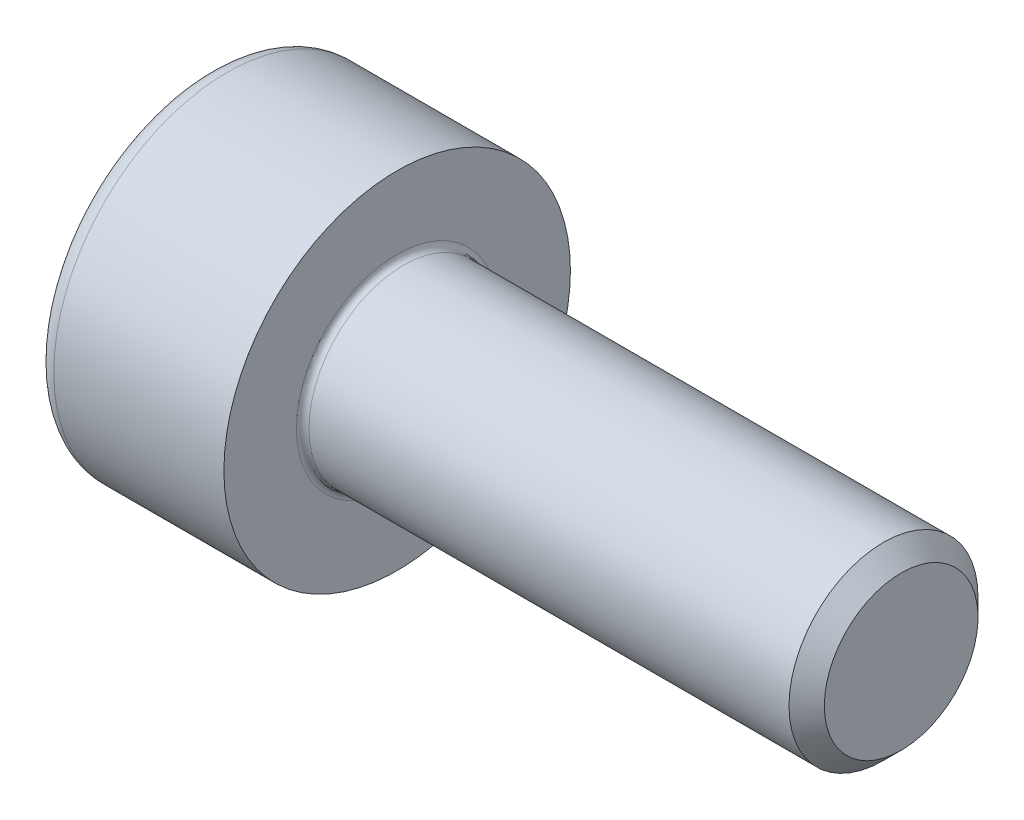
SolidWorks part; units mm, degrees
revolve "Base-Revolve" add sketch "BodySke"
sketch "BodySke" plane through (0, 0, 0) normal (0, 0, 1) x (1, 0, 0)
  line L0 (0, 0) -> (0, 2.75)
  line L1 (0, 2.75) -> (3, 2.75)
  line L2 (3, 2.75) -> (3, 1.5)
  line L3 (3, 1.5) -> (10.7195, 1.5)
  line L4 (11, 1.2195) -> (11, 0)
  line L5 (11, 0) -> (0, 0)
  line L6 (-31.75, 0) -> (127, 0) construction
  line L8 (11, 1.2195) -> (10.7195, 1.5)
  line L10 (11, -1.2195) -> (10.7195, -1.5) construction
  line L11 (3.5, 9.525) -> (3.5, 3.175) construction
  line L12 (6, 9.525) -> (6, 3.175) construction
  line L13 (-49, 9.525) -> (-49, 3.175) construction
  dimension "Head_ht" = 3
  dimension "Length" = 8
  dimension "Body_ch_ang" = 45
  dimension "Diameter" = 3
  dimension "Minor_dia" = 2.439
  dimension "Advance" = 0.5
  dimension "Thread_nom" = 5
  dimension "Thread_length" = 60
  dimension "Head_dia" = 5.5
cosmetic thread "ThreadCosmetic" [suppressed]
fillet "Fillet1" radius 0.1 1 edges at (3, 0, 1.5)
fillet "Fillet2" radius 0.3 1 edges at (0, 0, 2.75)
ref_plane "Plane1" through (0, 0, 0) normal (0, 0, 1) x (1, 0, 0)
ref_plane "Plane2" through (0, 0, 0) normal (0, 1, 0) x (1, 0, 0)
ref_plane "Plane3" through (0, 0, 0) normal (1, 0, 0) x (0, 0, -1)
other "Configuration Table"
sketch "Sketch2" plane through (0, 0, 0) normal (0, 0, 1) x (1, 0, 0)
  line L0 (0, 1.26) -> (1.3, 1.26)
  line L1 (1.3, 1.26) -> (2.0275, 0)
  line L2 (-31.75, 0) -> (127, 0) construction
  line L3 (2.0275, 0) -> (0, 0)
  line L4 (0, 0) -> (0, 1.26)
  line L6 (0, 0) -> (47.625, 0) construction
  dimension "D1" = 1.26
  dimension "D2" = 60
  dimension "Depth" = 1.3
revolve "Hex-PreBroach" cut sketch "Sketch2" angle 360 about L6
sketch "Sketch3" plane through (0, 0, 0) normal (-1, 0, 0) x (0, 0.5, 0.866)
  line L0 (0.7275, 1.26) -> (-0.7275, 1.26)
  line L1 (-0.7275, 1.26) -> (-1.4549, 0)
  line L2 (0.7275, 1.26) -> (1.4549, 0)
  line L3 (0.7275, -1.26) -> (1.4549, 0)
  line L4 (0.7275, -1.26) -> (-0.7275, -1.26)
  line L5 (-0.7275, -1.26) -> (-1.4549, 0)
  dimension "D1" = 1.26
  dimension "D2" = 1.26
  dimension "Hex_size" = 2.52
extrude "Hex" cut sketch "Sketch3" against normal blind 1.3
sketch "ThdSchSke" plane through (0, 0, 0) normal (0, 0, 1) x (1, 0, 0)
  line L0 (6, -1.2195) -> (5.8036, -1.5)
  line L1 (6, -1.2195) -> (6.1964, -1.5)
  line L2 (6.1964, -1.5) -> (6.1964, -1.875)
  line L3 (-3.175, 0) -> (5.1513, 0) construction
  line L4 (0, 2.45) -> (0, -2.45) construction
  line L5 (6.1964, -1.875) -> (5.8036, -1.875)
  line L6 (5.8036, -1.875) -> (5.8036, -1.5)
  dimension "Thread_minor" = 2.439
  dimension "Diameter" = 3
  dimension "Start" = 6
revolve "ThreadSchematic" [suppressed] cut sketch "ThdSchSke" angle 360 about L3
pattern_linear "ThdSchPat" [suppressed]
equation "\"D2@Sketch3\" = \"Hex_size@Sketch3\" / 2"
equation "\"D1@Sketch3\" = \"Hex_size@Sketch3\" / 2"
equation "\"D1@Sketch2\" = \"Hex_size@Sketch3\" / 2"
equation "\"Thread_minor@ThreadCosmetic\"  =  \"Minor_dia@BodySke\""
equation "\"Depth@Sketch2\" =  \"Key_eng@Hex\""
equation "\"Thread_length@ThreadCosmetic\" = ((sgn( (\"Length@BodySke\" - \"Advance@BodySke\" * 3.0) - \"Thread_nom@BodySke\" )-1)*( (\"Length@BodySke\" - \"Advance@BodySke\" * 3.0) - \"Thread_nom@BodySke\" ))/-2+ \"Thread_nom@BodySke\""
equation "\"Thread_minor@ThdSchSke\" = \"Minor_dia@BodySke\""
equation "\"Diameter@ThdSchSke\" = \"Diameter@BodySke\""
equation "\"Overcut@ThdSchSke\" = \"Diameter@BodySke\" * 1.25"
equation "\"Start@ThdSchSke\" = \"Head_ht@BodySke\" + \"Length@BodySke\" - \"Thread_length@ThreadCosmetic\"  '---Non-countersunk---"
equation "\"Num_threads@ThdSchPat\" = int( \"Thread_length@ThreadCosmetic\" / \"Advance@BodySke\" + 0.999 )  + 1"
equation "\"Advance@ThdSchPat\" = \"Thread_length@ThreadCosmetic\" /  (\"Num_threads@ThdSchPat\" - 1) 'relax it"
equation "\"Num_threads@ThdSchPat\" = \"Num_threads@ThdSchPat\" - sgn( \"Num_threads@ThdSchPat\" - 1) '---chamfered tips only---"
